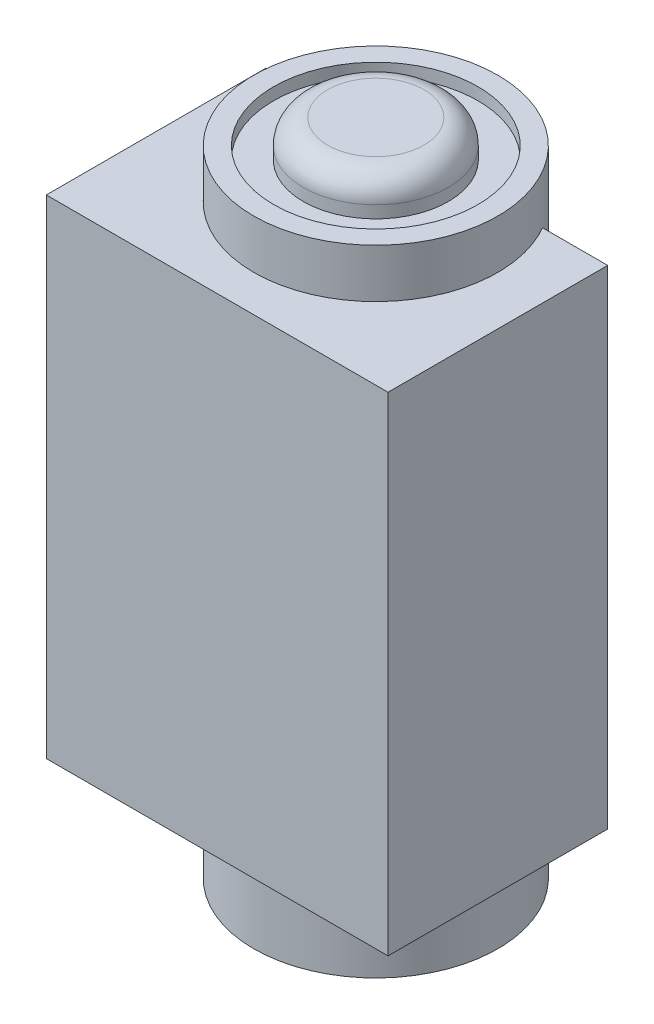
SolidWorks part; units mm, degrees
ref_plane "Front Plane" through (0, 0, 0) normal (0, 0, 1) x (1, 0, 0)
ref_plane "Top Plane" through (0, 0, 0) normal (0, 1, 0) x (1, 0, 0)
ref_plane "Right Plane" through (0, 0, 0) normal (1, 0, 0) x (0, 0, -1)
sketch "Sketch1" plane through (0, 0, 0) normal (0, 1, 0) x (1, 0, 0)
  line L0 (-4.3301, 4.5) -> (-7, 4.5)
  line L1 (7, -4.5) -> (-7, -4.5)
  line L2 (7, -4.5) -> (7, 4.5)
  line L3 (7, 4.5) -> (4.3301, 4.5)
  line L4 (-7, -4.5) -> (-7, 4.5)
  line L5 (7, -4.5) -> (-7, 4.5) construction
  line L6 (7, 4.5) -> (-7, -4.5) construction
  arc A0 (-4.3301, 4.5) -> (4.3301, 4.5) centre (0, 2) ccw
  point P0 (0, 0)
  dimension "D2" = 10
  dimension "D4" = 6.5
  dimension "D1" = 14
  dimension "D3" = 9
extrude "Boss-Extrude1" add sketch "Sketch1" along normal blind 20
sketch "Sketch2" plane through (0, 0, 0) normal (0, 1, 0) x (1, 0, 0)
  circle A0 centre (0, 2) radius 5
  arc A1 (-4.3301, 4.5) -> (4.3301, 4.5) centre (0, 2) ccw construction
extrude "Boss-Extrude2" add sketch "Sketch2" along normal blind 26 from offset 4 separate body offset against normal yes
sketch "Sketch3" plane through (0, 22, 0) normal (0, 1, 0) x (1, 0, 0)
  circle A0 centre (0, 2) radius 4.1863
extrude "Cut-Extrude1" cut sketch "Sketch3" against normal blind 0.5
sketch "Sketch4" plane through (0, 21.5, 0) normal (0, 1, 0) x (1, 0, 0)
  circle A0 centre (0, 2) radius 2.9714
extrude "Boss-Extrude3" add sketch "Sketch4" along normal blind 1.5
fillet "Fillet1" radius 1 1 edges at (0, 23, 0.9714)
sketch "Sketch5" plane through (0, -4, 0) normal (0, -1, 0) x (1, 0, 0)
  circle A0 centre (0, -2) radius 4.4052
extrude "Cut-Extrude2" cut sketch "Sketch5" against normal blind 0.25
sketch "Sketch6" plane through (0, -3.75, 0) normal (0, -1, 0) x (1, 0, 0)
  circle A0 centre (0, -2) radius 4.1912
extrude "Boss-Extrude4" add sketch "Sketch6" along normal blind 0.25 separate body
